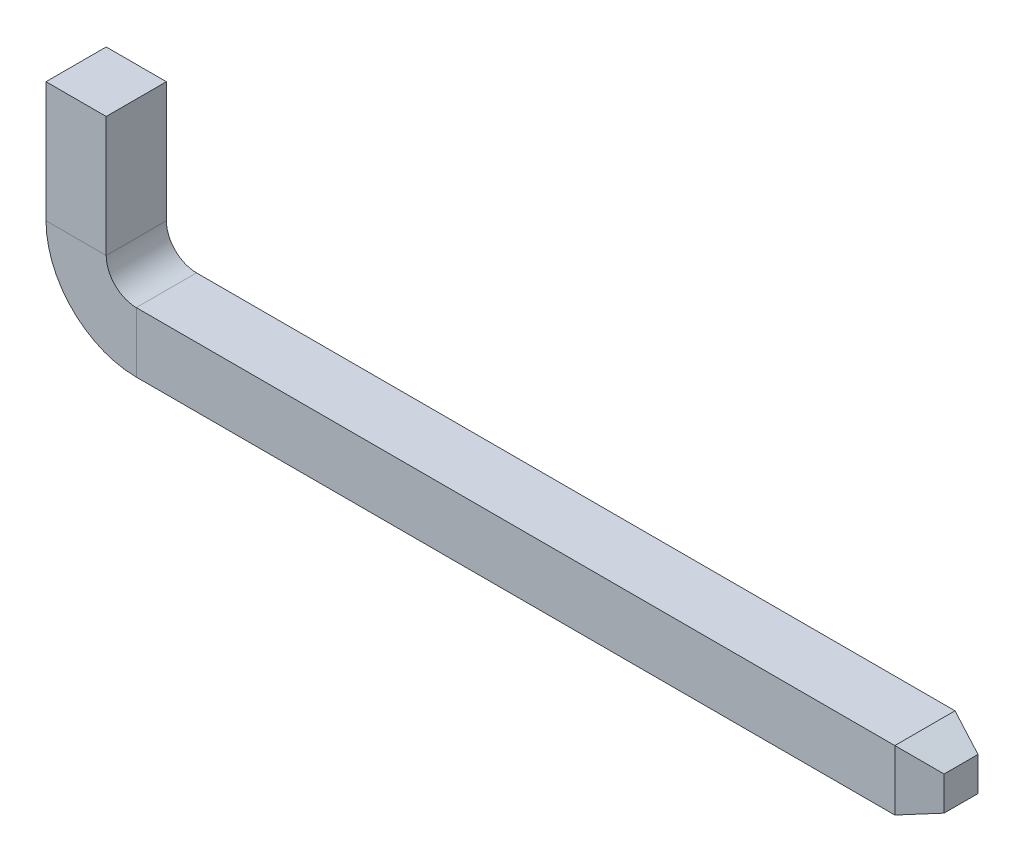
SolidWorks part; units mm, degrees
ref_plane "Front Plane" through (0, 0, 0) normal (0, 0, 1) x (1, 0, 0)
ref_plane "Top Plane" through (0, 0, 0) normal (0, 1, 0) x (1, 0, 0)
ref_plane "Right Plane" through (0, 0, 0) normal (1, 0, 0) x (0, 0, -1)
sketch "Sketch1" plane through (0, 0, 0) normal (0, 1, 0) x (1, 0, 0)
  line L1 (-0.25, -0.25) -> (0.25, -0.25)
  line L2 (-0.25, -0.25) -> (-0.25, 0.25)
  line L3 (-0.25, 0.25) -> (0.25, 0.25)
  line L4 (0.25, -0.25) -> (0.25, 0.25)
  line L5 (-0.25, -0.25) -> (0.25, 0.25) construction
  line L6 (-0.25, 0.25) -> (0.25, -0.25) construction
  point P0 (0, 0)
  dimension "D1" = 0.5
sketch "Sketch2" plane through (0, 0, 0) normal (0, 0, 1) x (1, 0, 0)
  line L0 (0, 0) -> (0, -1)
  line L1 (0.5, -1.5) -> (6.8, -1.5)
  arc A0 (0, -1) -> (0.5, -1.5) centre (0.5, -1) ccw
  point P6 (0, -1.5)
  dimension "D3" = 0.5
  dimension "D1" = 1.5
  dimension "D2" = 6.8
ref_plane "Plane1" through (6.8, 0, 0) normal (1, 0, 0) x (0, 0, -1)
sweep "Sweep1" add profiles "Sketch1" path "Sketch2"
sketch "Sketch4" plane through (6.8, 0, 0) normal (1, 0, 0) x (0, 0, -1)
  line L4 (0.25, -1.25) -> (-0.25, -1.25)
  line L5 (-0.25, -1.25) -> (-0.25, -1.75)
  line L6 (-0.25, -1.75) -> (0.25, -1.75)
  line L7 (0.25, -1.75) -> (0.25, -1.25)
  line L8 (0.25, -1.25) -> (-0.25, -1.25)
  line L9 (-0.25, -1.25) -> (-0.25, -1.75)
  line L10 (-0.25, -1.75) -> (0.25, -1.75)
  line L11 (0.25, -1.75) -> (0.25, -1.25)
  dimension "D1" = 0
extrude "Boss-Extrude1" add sketch "Sketch4" along normal blind 0.3 draft 20
